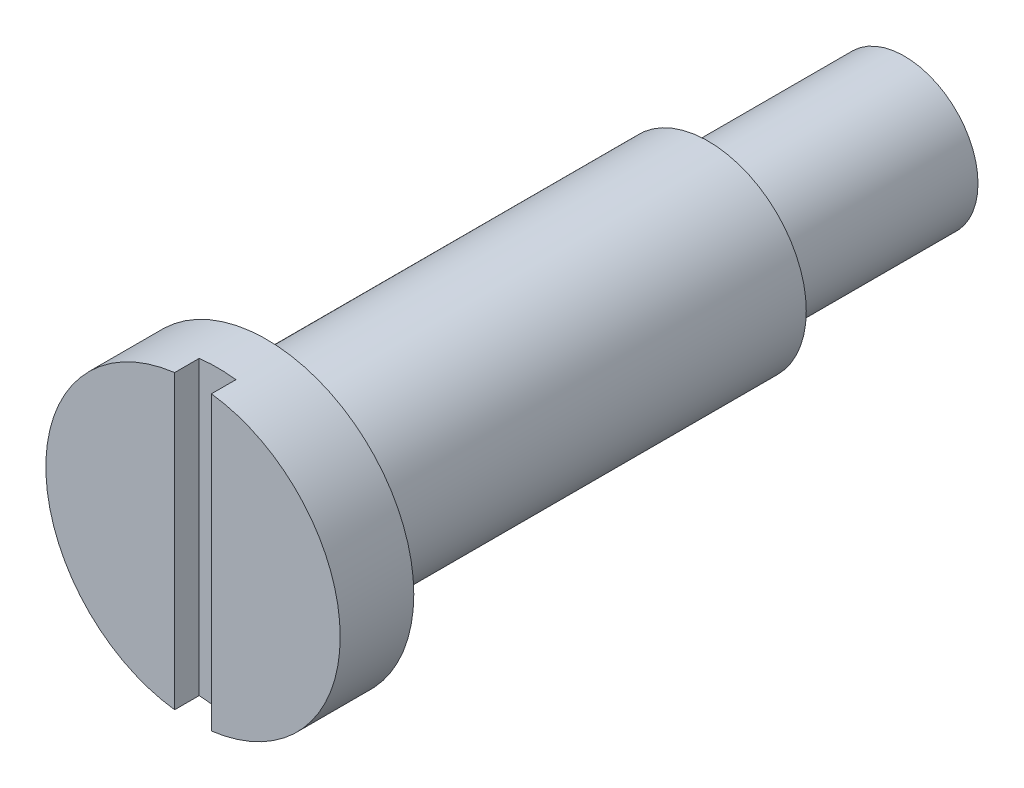
SolidWorks part; units mm, degrees
ref_plane "前视基准面" through (0, 0, 0) normal (0, 0, 1) x (1, 0, 0)
ref_plane "上视基准面" through (0, 0, 0) normal (0, 1, 0) x (1, 0, 0)
ref_plane "右视基准面" through (0, 0, 0) normal (1, 0, 0) x (0, 0, -1)
sketch "草图2" plane through (0, 0, 0) normal (1, 0, 0) x (0, 0, -1)
  line L0 (0, 0) -> (105.7683, 0) construction
  line L1 (0, 0) -> (0, 6)
  line L2 (0, 6) -> (3, 6)
  line L3 (3, 6) -> (3, 4)
  line L4 (3, 4) -> (21, 4)
  line L5 (21, 4) -> (21, 3)
  line L6 (0, 0) -> (29, 0)
  line L7 (21, 3) -> (29, 3)
  line L8 (29, 3) -> (29, 0)
  dimension "D1" = 12
  dimension "D2" = 18
  dimension "D3" = 3
  dimension "D4" = 8
  dimension "D5" = 6
  dimension "D6" = 8
revolve "旋转1" add sketch "草图2" angle 360 about L0
cosmetic thread "装饰螺纹线1" parameters "D2"=5
sketch "草图3" plane through (0, 0, 0) normal (0, 0, 1) x (1, 0, 0)
  line L0 (0, 6) -> (0, -6) construction
  line L2 (-0.75, 6) -> (0.75, 6)
  line L3 (-0.75, 6) -> (-0.75, -6)
  line L4 (-0.75, -6) -> (0.75, -6)
  line L5 (0.75, 6) -> (0.75, -6)
  circle A0 centre (0, 0) radius 6 construction
  dimension "D1" = 1.5
extrude "切除-拉伸1" cut sketch "草图3" against normal blind 1
